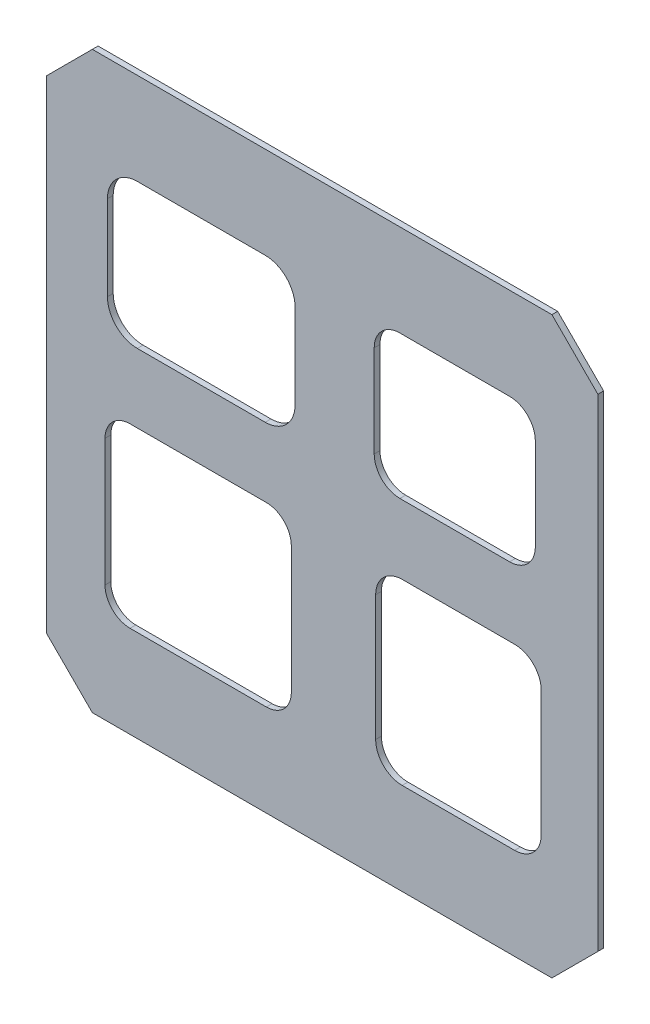
SolidWorks part; units mm, degrees
ref_plane "Front Plane" through (0, 0, 0) normal (0, 0, 1) x (1, 0, 0)
ref_plane "Top Plane" through (0, 0, 0) normal (0, 1, 0) x (1, 0, 0)
ref_plane "Right Plane" through (0, 0, 0) normal (1, 0, 0) x (0, 0, -1)
sketch "Sketch1" plane through (0, 0, 0) normal (0, 0, 1) x (1, 0, 0)
  line L0 (0, 266.7) -> (25.4, 292.1)
  line L2 (0, 0) -> (0, 266.7)
  line L4 (304.8, 0) -> (304.8, 266.7)
  line L5 (304.8, 266.7) -> (279.4, 292.1)
  line L6 (25.4, 292.1) -> (279.4, 292.1)
  line L7 (0, 0) -> (25.4, -25.4)
  line L8 (304.8, 0) -> (279.4, -25.4)
  line L9 (25.4, -25.4) -> (279.4, -25.4)
  line L10 (0, 133.35) -> (304.8, 133.35) construction
  dimension "D1" = 304.8
  dimension "D2" = 266.7
  dimension "D4" = 25.4
  dimension "D5" = 25.4
  dimension "D6" = 254
  dimension "D7" = 25.4
  dimension "D8" = 25.4
  dimension "D9" = 25.4
extrude "Boss-Extrude1" add sketch "Sketch1" along normal blind 3.175
sketch "Sketch4" plane through (0, 0, 3.175) normal (0, 0, 1) x (1, 0, 0)
  line L0 (279.4, 292.1) -> (25.4, 292.1) construction
  line L1 (50.2589, 241.3) -> (120.9334, 241.3)
  line L2 (33.7489, 224.79) -> (33.7489, 177.8757)
  line L3 (50.2589, 161.3657) -> (120.9334, 161.3657)
  line L4 (137.4434, 224.79) -> (137.4434, 177.8757)
  line L5 (195.3668, 241.3) -> (256.0355, 241.3)
  line L6 (181.1753, 227.1085) -> (181.1753, 176.3085)
  line L7 (195.3668, 162.117) -> (256.0355, 162.117)
  line L8 (270.227, 227.1085) -> (270.227, 176.3085)
  line L9 (121.1458, 123.2657) -> (46.2369, 123.2657)
  line L10 (135.3752, 109.4416) -> (135.3752, 39.2241)
  line L11 (121.5511, 25.4) -> (46.2369, 25.4)
  line L12 (32.4128, 109.4416) -> (32.4128, 39.2241)
  line L13 (196.6448, 124.017) -> (258.8156, 124.017)
  line L14 (181.9833, 109.3555) -> (181.9833, 40.0615)
  line L15 (196.6448, 25.4) -> (258.8156, 25.4)
  line L16 (273.4771, 109.3555) -> (273.4771, 40.0615)
  line L17 (25.4, -25.4) -> (279.4, -25.4) construction
  arc A0 (33.7489, 224.79) -> (50.2589, 241.3) centre (50.2589, 224.79) cw
  arc A1 (120.9334, 241.3) -> (137.4434, 224.79) centre (120.9334, 224.79) cw
  arc A2 (137.4434, 177.8757) -> (120.9334, 161.3657) centre (120.9334, 177.8757) cw
  arc A3 (33.7489, 177.8757) -> (50.2589, 161.3657) centre (50.2589, 177.8757) ccw
  arc A4 (195.3668, 241.3) -> (181.1753, 227.1085) centre (195.3668, 227.1085) ccw
  arc A5 (256.0355, 241.3) -> (270.227, 227.1085) centre (256.0355, 227.1085) cw
  arc A6 (270.227, 176.3085) -> (256.0355, 162.117) centre (256.0355, 176.3085) cw
  arc A7 (181.1753, 176.3085) -> (195.3668, 162.117) centre (195.3668, 176.3085) ccw
  arc A8 (121.1458, 123.2657) -> (135.3752, 109.4416) centre (121.5511, 109.4476) cw
  arc A9 (135.3752, 39.2241) -> (121.5511, 25.4) centre (121.5511, 39.2241) cw
  arc A10 (32.4128, 39.2241) -> (46.2369, 25.4) centre (46.2369, 39.2241) ccw
  arc A11 (46.2369, 123.2657) -> (32.4128, 109.4416) centre (46.2369, 109.4416) ccw
  arc A12 (196.6448, 124.017) -> (181.9833, 109.3555) centre (196.6448, 109.3555) ccw
  arc A13 (181.9833, 40.0615) -> (196.6448, 25.4) centre (196.6448, 40.0615) ccw
  arc A14 (273.4771, 40.0615) -> (258.8156, 25.4) centre (258.8156, 40.0615) cw
  arc A15 (258.8156, 124.017) -> (273.4771, 109.3555) centre (258.8156, 109.3555) cw
  dimension "D8" = 14.1915
  dimension "D10" = 16.51
  dimension "D1" = 50.8
  dimension "D2" = 50.8
  dimension "D3" = 50.8
  dimension "D4" = 50.8
  dimension "D5" = 38.1
  dimension "D6" = 38.1
  dimension "D7" = 50.8
  dimension "D9" = 43.7319
extrude "Cut-Extrude7" cut sketch "Sketch4" against normal blind 127
